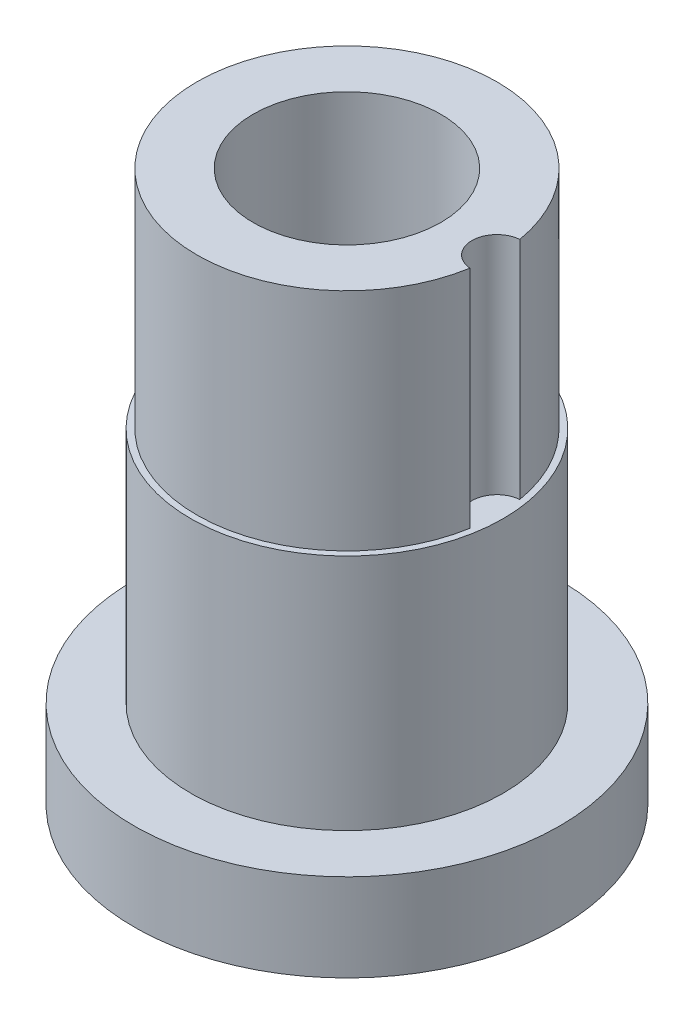
SolidWorks part; units mm, degrees
ref_plane "Front Plane" through (0, 0, 0) normal (0, 0, 1) x (1, 0, 0)
ref_plane "Top Plane" through (0, 0, 0) normal (0, 1, 0) x (1, 0, 0)
ref_plane "Right Plane" through (0, 0, 0) normal (1, 0, 0) x (0, 0, -1)
sketch "Sketch1" plane through (0, 0, 0) normal (0, 0, 1) x (1, 0, 0)
  line L0 (0, -34.925) -> (0, 34.925) construction
  line L1 (15.0813, -34.925) -> (26.9875, -34.925)
  line L2 (26.9875, -34.925) -> (26.9875, -23.8125)
  line L3 (26.9875, -23.8125) -> (19.812, -23.8125)
  line L4 (19.812, -23.8125) -> (19.812, 6.35)
  line L5 (19.0246, 6.35) -> (19.0246, 34.925)
  line L6 (19.0246, 34.925) -> (11.9062, 34.925)
  line L7 (11.9062, 34.925) -> (11.9062, 3.175)
  line L8 (15.0812, 0) -> (15.0813, -34.925)
  line L9 (19.0246, 6.35) -> (19.812, 6.35)
  arc A0 (11.9062, 3.175) -> (15.0812, 0) centre (11.9062, 0) cw
  point P3 (0, 0)
  point P14 (11.9063, 32.9411)
  point P15 (11.9063, 34.925)
  point P16 (15.0813, -4.2374)
  dimension "D2" = 15.0812
  dimension "D8" = 3.175
  dimension "D1" = 69.85
  dimension "D3" = 26.9875
  dimension "D4" = 11.1125
  dimension "D5" = 30.1625
  dimension "D6" = 19.812
  dimension "D7" = 19.0246
  dimension "D9" = 38.1
revolve "Revolve1" add sketch "Sketch1" angle 360 about L0
sketch "Sketch2" plane through (0, 34.925, 0) normal (0, 1, 0) x (1, 0, 0)
  circle A0 centre (19.0246, 0) radius 3.175
  circle A1 centre (0, 0) radius 19.0246 construction
  circle A2 centre (0, 0) radius 19.0246 construction
  point P6 (18.6786, -3.6121)
  dimension "D1" = 6.35
extrude "Cut-Extrude1" cut sketch "Sketch2" against normal up to surface (28.575 mm away) up to face at (19.0246, 6.35, 0)
